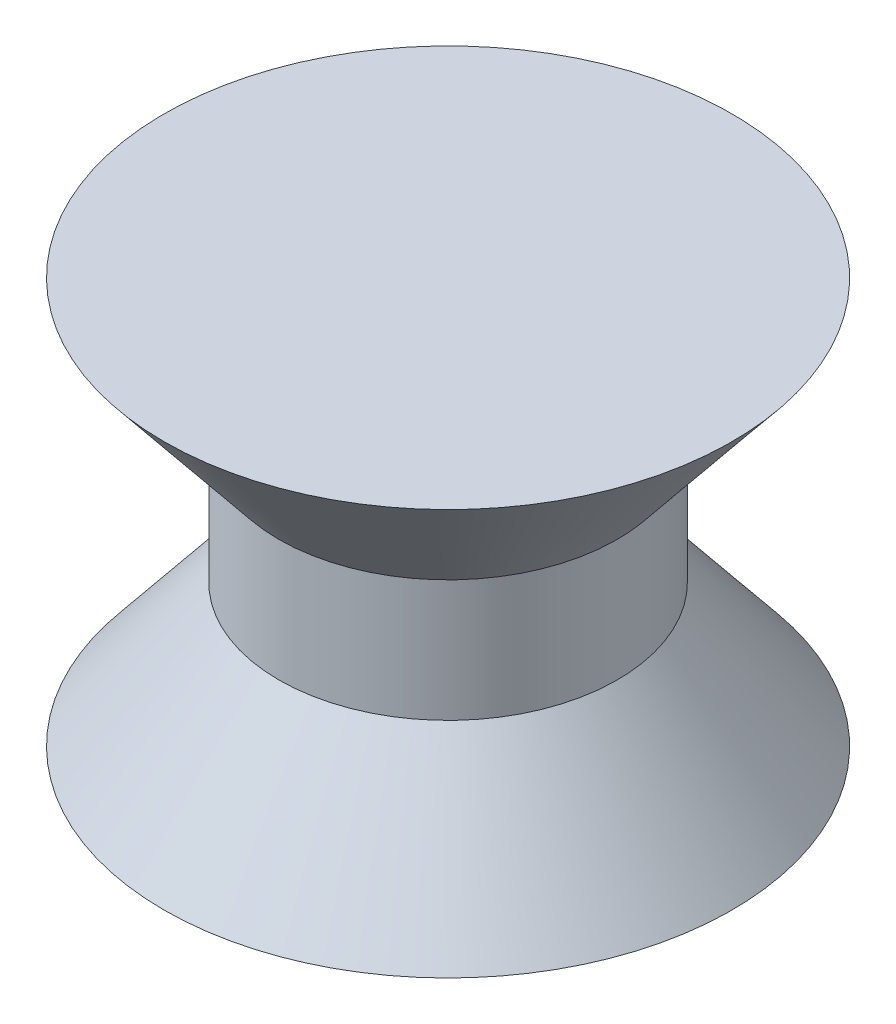
SolidWorks part; units mm, degrees
ref_plane "Alzado" through (0, 0, 0) normal (0, 0, 1) x (1, 0, 0)
ref_plane "Planta" through (0, 0, 0) normal (0, 1, 0) x (1, 0, 0)
ref_plane "Vista lateral" through (0, 0, 0) normal (1, 0, 0) x (0, 0, -1)
sketch "Croquis1" plane through (0, 0, 0) normal (0, 0, 1) x (1, 0, 0)
  line L0 (0, 14.0566) -> (0, -16.4694) construction
  line L1 (-7.0807, 0) -> (8.1323, 0) construction
  line L12 (0, 5) -> (0, -5)
  line L13 (0, 5) -> (7, 5)
  line L14 (0, -5) -> (7, -5)
  line L15 (7, -5) -> (4.1724, -1.5)
  line L16 (7, 5) -> (4.1724, 1.5)
  line L17 (4.1724, 1.5) -> (4.1724, -1.5)
  dimension "D1" = 10
  dimension "D2" = 5
  dimension "D3" = 7
  dimension "D4" = 1.5
  dimension "D5" = 3
  dimension "D6" = 4.4995
  dimension "D7" = 5.446
  dimension "D8" = 4.4995
revolve "Revolución3" add sketch "Croquis1" angle 360 about L0
ref_plane "Plano1" through (0, -5, 0) normal (0, -1, 0) x (-1, 0, 0)
sketch "Croquis2" plane through (0, -5, 0) normal (0, -1, 0) x (-1, 0, 0)
  line L0 (0, 7) -> (0, -7) construction
  line L1 (-7, 0) -> (7, 0) construction
  circle A0 centre (0, 0) radius 7 construction
  circle A1 centre (0, 0) radius 1.5
  dimension "D1" = 3
extrude "Cortar-Extruir1" cut sketch "Croquis2" against normal blind 2
